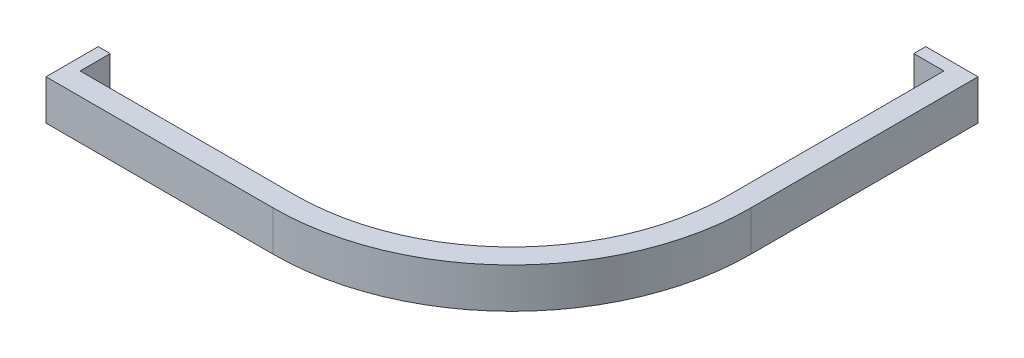
SolidWorks part; units mm, degrees
ref_plane "Front Plane" through (0, 0, 0) normal (0, 0, 1) x (1, 0, 0)
ref_plane "Top Plane" through (0, 0, 0) normal (0, 1, 0) x (1, 0, 0)
ref_plane "Right Plane" through (0, 0, 0) normal (1, 0, 0) x (0, 0, -1)
sketch "Sketch1" plane through (0, 0, 0) normal (0, 1, 0) x (1, 0, 0)
  line L0 (0, 0) -> (0, -145.5772) construction
  line L1 (-56.57, -56.57) -> (56.57, -56.57) construction
  line L2 (-56.57, -56.57) -> (-56.57, 56.57) construction
  line L3 (-56.57, 56.57) -> (56.57, 56.57) construction
  line L4 (56.57, -56.57) -> (56.57, 56.57) construction
  line L5 (-56.57, -56.57) -> (56.57, 56.57) construction
  line L6 (-56.57, 56.57) -> (56.57, -56.57) construction
  line L7 (0, 0) -> (166.7552, 0) construction
  line L8 (0, -116.07) -> (56.57, -116.07)
  line L9 (116.07, -56.57) -> (116.07, 0)
  line L10 (116.07, 0) -> (103.07, 0)
  line L13 (0, -103.07) -> (0, -116.07)
  line L14 (56.57, -110.57) -> (3, -110.57)
  line L15 (3, -110.57) -> (3, -103.07)
  line L16 (3, -103.07) -> (0, -103.07)
  line L17 (110.57, -56.57) -> (110.57, -3)
  line L18 (110.57, -3) -> (103.07, -3)
  line L19 (103.07, -3) -> (103.07, 0)
  circle A0 centre (56.57, -56.57) radius 55 construction
  circle A1 centre (-56.57, -56.57) radius 55 construction
  arc A2 (56.57, -116.07) -> (116.07, -56.57) centre (56.57, -56.57) ccw
  arc A3 (110.57, -56.57) -> (56.57, -110.57) centre (56.57, -56.57) cw
  point P0 (0, 0)
  dimension "D1" = 110
  dimension "D2" = 113.14
  dimension "D3" = 1
  dimension "D4" = 4.5
  dimension "D5" = 3
  dimension "D6" = 13
extrude "Boss-Extrude1" add sketch "Sketch1" along normal blind 10
